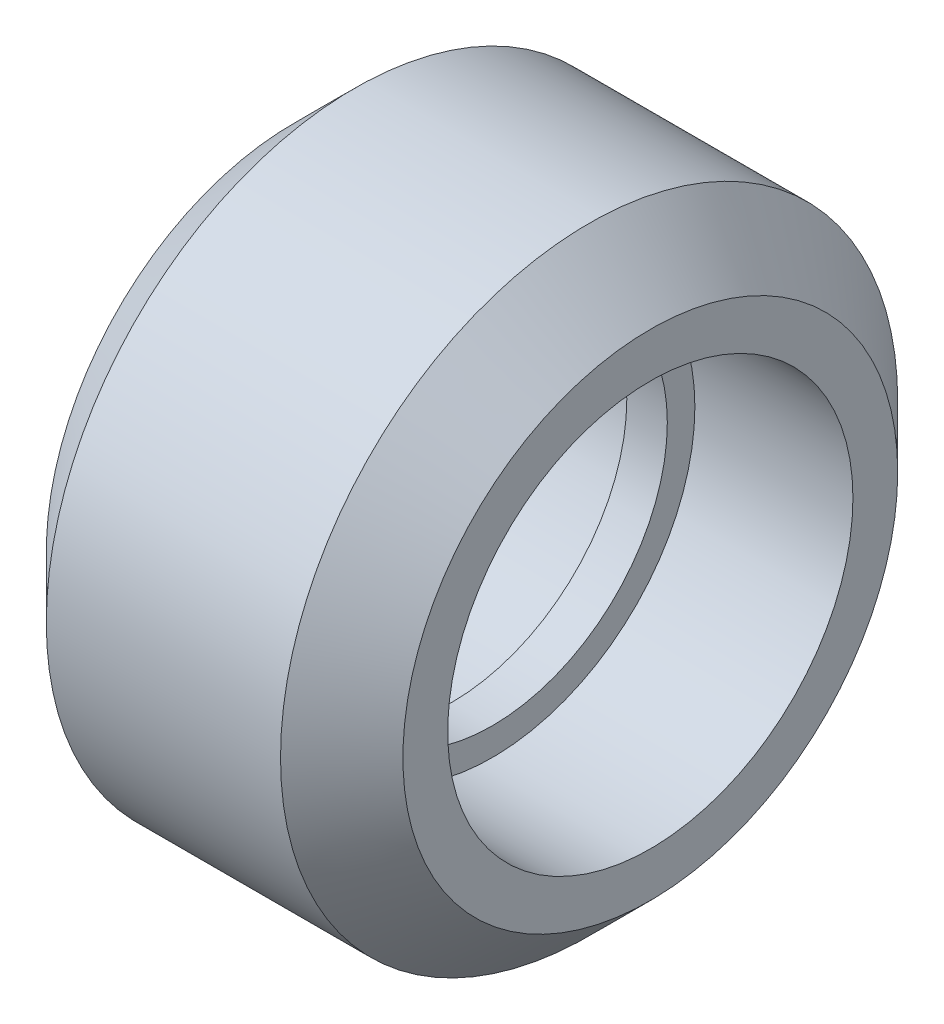
SolidWorks part; units mm, degrees
material "Delrin 2700 NC010, Low Viscosity Acetal Copolymer (SS)"
ref_plane "Front Plane" through (0, 0, 0) normal (0, 0, 1) x (1, 0, 0)
ref_plane "Top Plane" through (0, 0, 0) normal (0, 1, 0) x (1, 0, 0)
ref_plane "Right Plane" through (0, 0, 0) normal (1, 0, 0) x (0, 0, -1)
sketch "Sketch1" plane through (0, 0, 0) normal (0, 0, 1) x (1, 0, 0)
  line L0 (0.5, 4.32) -> (-0.5, 4.32)
  line L1 (-0.5, 4.32) -> (-0.5, 5)
  line L2 (-0.5, 5) -> (-4.4, 5)
  line L3 (-4.4, 5) -> (-4.4, 6.105)
  line L4 (-4.4, 6.105) -> (-2.89, 7.615)
  line L5 (-2.89, 7.615) -> (2.89, 7.615)
  line L6 (0, 7.615) -> (0, 4.32) construction
  line L7 (4.4, 6.105) -> (2.89, 7.615)
  line L8 (4.4, 5) -> (4.4, 6.105)
  line L9 (0.5, 5) -> (4.4, 5)
  line L10 (0.5, 4.32) -> (0.5, 5)
  line L11 (0, 0) -> (-12.6359, 0) construction
  dimension "D1" = 12.21
  dimension "8.64" = 8.64
  dimension "D2" = 10
  dimension "D3" = 15.23
  dimension "D4" = 1
  dimension "D5" = 45
  dimension "D6" = 8.8
  dimension "D7" = 5.78
revolve "Revolve1" add sketch "Sketch1" angle 360 about L11
move or copy body "Sólido-Mover/Copiar1" [suppressed] bodies to move or copy 101
